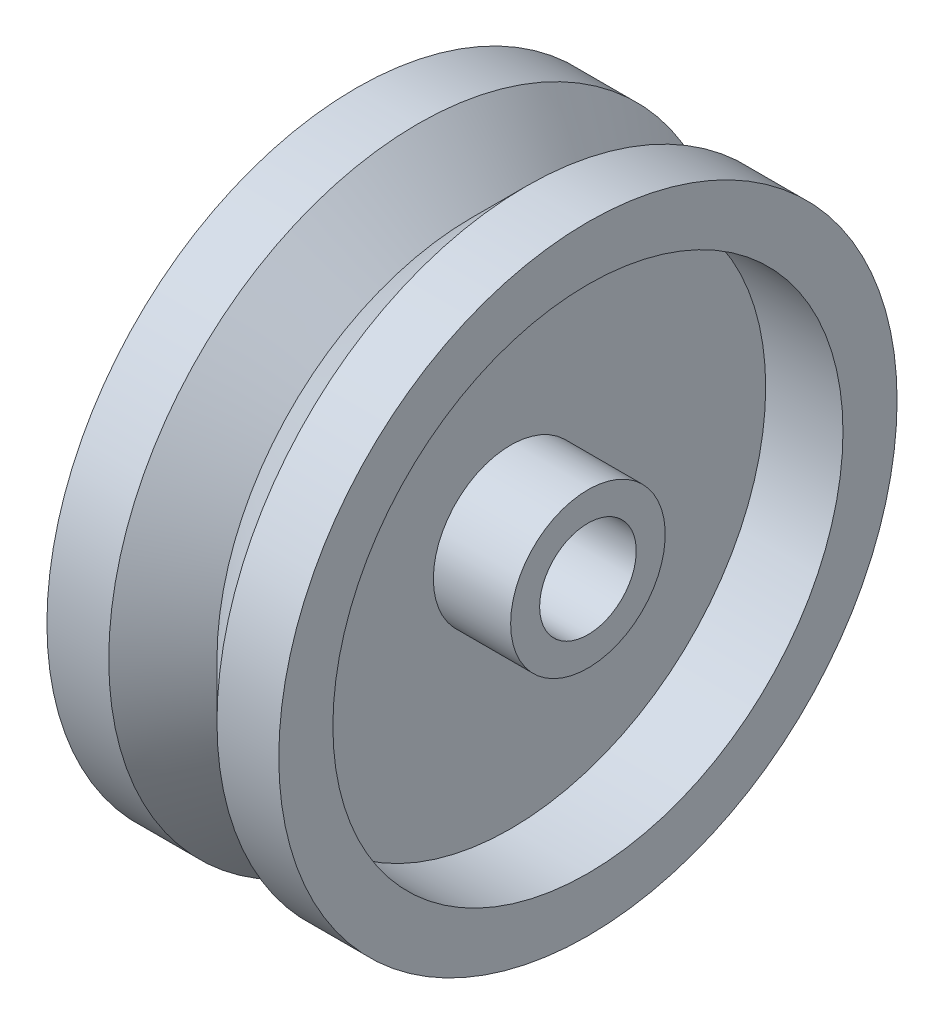
SolidWorks part; units mm, degrees
ref_plane "Front Plane" through (0, 0, 0) normal (0, 0, 1) x (1, 0, 0)
ref_plane "Top Plane" through (0, 0, 0) normal (0, 1, 0) x (1, 0, 0)
ref_plane "Right Plane" through (0, 0, 0) normal (1, 0, 0) x (0, 0, -1)
sketch "Sketch1" plane through (0, 0, 0) normal (0, 0, 1) x (1, 0, 0)
  line L0 (0, 64.2446) -> (0, -42.7742) construction
  line L1 (-66.3693, 0) -> (79.5573, 0) construction
  line L2 (-7.5, 3.125) -> (7.5, 3.125)
  line L3 (7.5, 3.125) -> (7.5, 5)
  line L4 (7.5, 20) -> (3.5, 20)
  line L5 (3.5, 20) -> (0, 16.5)
  line L6 (0, 16.5) -> (-3.5, 20)
  line L7 (-3.5, 20) -> (-7.5, 20)
  line L8 (-7.5, 20) -> (-7.5, 16.5)
  line L9 (-7.5, 16.5) -> (-2.5, 16.5)
  line L10 (-2.5, 16.5) -> (-2.5, 5)
  line L11 (-2.5, 5) -> (-7.5, 5)
  line L12 (7.5, 16.5) -> (2.5, 16.5)
  line L13 (2.5, 16.5) -> (2.5, 5)
  line L14 (2.5, 5) -> (7.5, 5)
  line L15 (-7.5, 5) -> (-7.5, 3.125)
  line L16 (7.5, 16.5) -> (7.5, 20)
  dimension "D1" = 90
  dimension "D2" = 5
  dimension "D3" = 4
  dimension "D4" = 15
  dimension "D5" = 3.125
  dimension "D6" = 5
  dimension "D7" = 16.5
  dimension "D8" = 20
revolve "Revolve1" add sketch "Sketch1" angle 360 about L1
